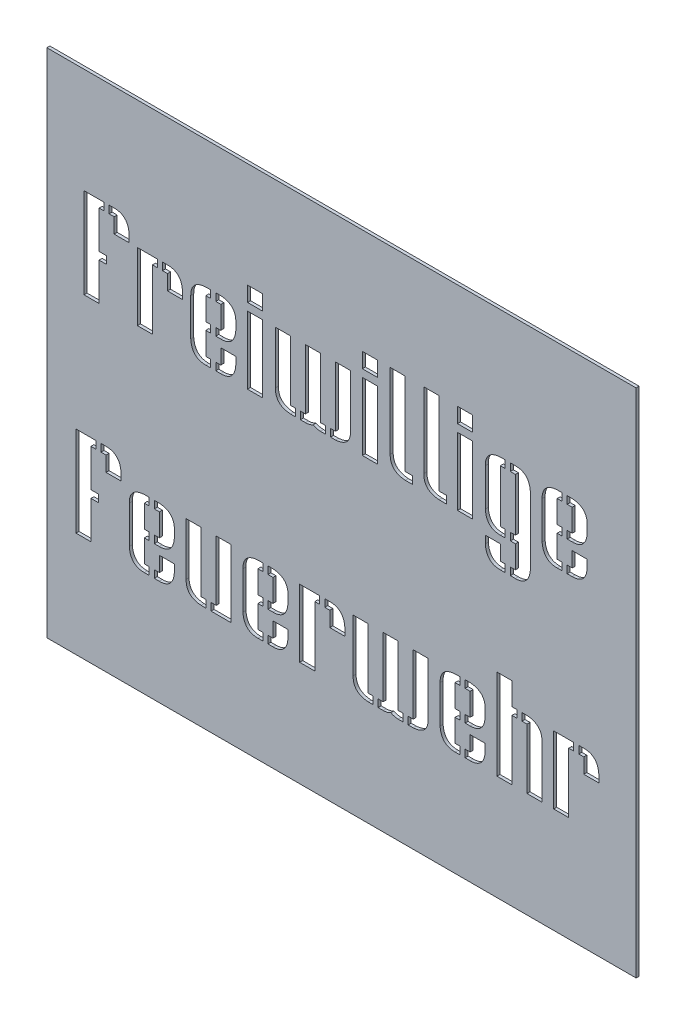
SolidWorks part; units mm, degrees
ref_plane "Ebene vorne" through (0, 0, 0) normal (0, 0, 1) x (1, 0, 0)
ref_plane "Ebene oben" through (0, 0, 0) normal (0, 1, 0) x (1, 0, 0)
ref_plane "Ebene rechts" through (0, 0, 0) normal (1, 0, 0) x (0, 0, -1)
sketch "Skizze1" plane through (0, 0, 0) normal (0, 0, 1) x (1, 0, 0)
  line L0 (0, 843.0467) -> (0, -846.9908) construction
  line L1 (-1046.1668, 0) -> (1345.9167, 0) construction
  line L3 (-490, 425) -> (490, 425)
  line L4 (-490, 425) -> (-490, -425)
  line L5 (-490, -425) -> (490, -425)
  line L6 (490, 425) -> (490, -425)
  dimension "D1" = 980
  dimension "D2" = 850
extrude "Aufsatz-Linear austragen1" add sketch "Skizze1" along normal blind 5
sketch "Skizze2" plane through (0, 0, 5) normal (0, 0, 1) x (1, 0, 0)
  line L0 (-490, 100) -> (490, 100)
  line L1 (-490, 425) -> (-490, -425) construction
  line L2 (490, -425) -> (490, 425) construction
  line L3 (-490, -250) -> (490, -250)
  line L4 (490, 425) -> (-490, 425) construction
  dimension "D1" = 325
  dimension "D2" = 350
sketch "Skizze3" plane through (0, 0, 5) normal (0, 0, 1) x (1, 0, 0)
  text T0 "Freiwillige" font "Soupertrouper Stencil" height 150
  text T1 "Feuerwehr" font "Soupertrouper Stencil" height 150
extrude "Schnitt-Linear austragen1" cut sketch "Skizze3" against normal through all
